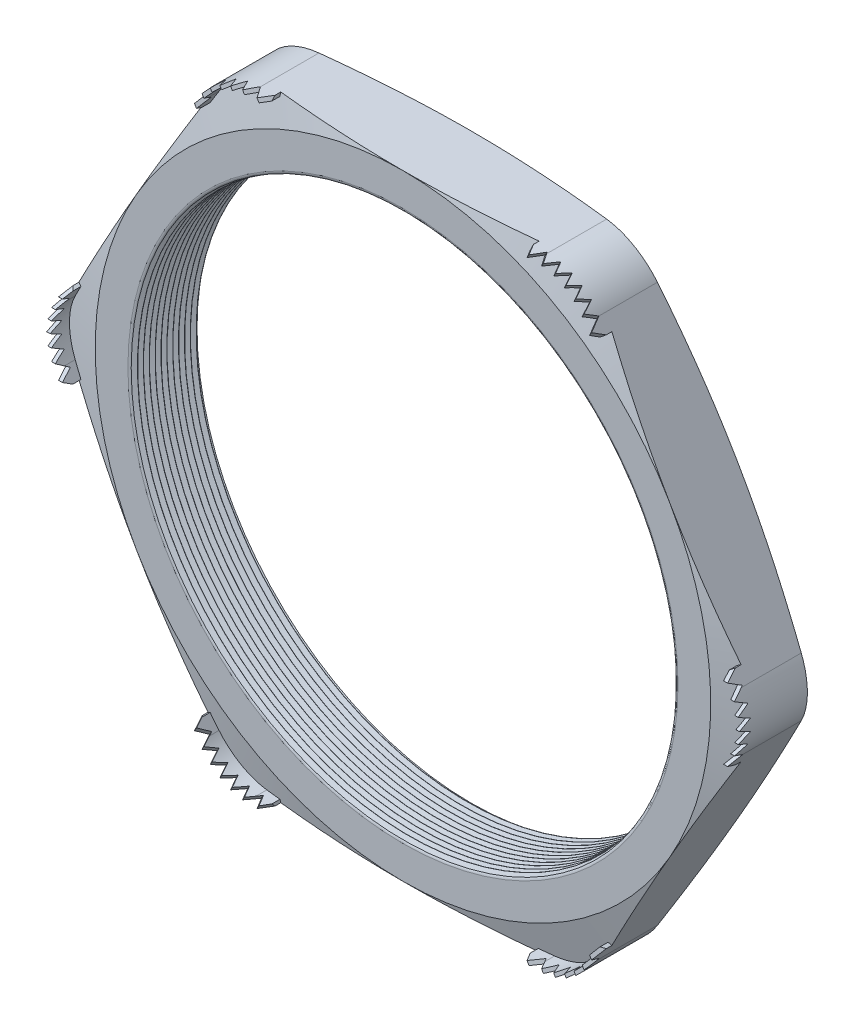
SolidWorks part; units mm, degrees
ref_plane "Front Plane" through (0, 0, 0) normal (0, 0, 1) x (1, 0, 0)
ref_plane "Top Plane" through (0, 0, 0) normal (0, 1, 0) x (1, 0, 0)
ref_plane "Right Plane" through (0, 0, 0) normal (1, 0, 0) x (0, 0, -1)
sketch "Sketch1" plane through (0, 0, 0) normal (0, 0, 1) x (1, 0, 0)
  line L1 (-18.4775, 0) -> (-9.2388, -16.002)
  line L2 (-9.2388, -16.002) -> (9.2388, -16.002)
  line L3 (9.2388, -16.002) -> (18.4775, 0)
  line L4 (18.4775, 0) -> (9.2388, 16.002)
  line L5 (9.2388, 16.002) -> (-9.2388, 16.002)
  line L6 (-9.2388, 16.002) -> (-18.4775, 0)
  circle A0 centre (0, 0) radius 16.002 construction
  circle A1 centre (0, 0) radius 14.097
  dimension "TS" = 28.194
  dimension "H" = 32.004
extrude "Extrude1" add sketch "Sketch1" along normal blind 3.556
fillet "Fillet1" radius 3.048 6 edges at (-9.2388, 16.002, 1.778) (-18.4775, 0, 1.778) (-9.2388, -16.002, 1.778) (9.2388, -16.002, 1.778) (18.4775, 0, 1.778) (9.2388, 16.002, 1.778)
sketch "Sketch2" plane through (0, 0, 3.556) normal (0, 0, 1) x (1, 0, 0)
  line L0 (-7.479, 16.002) -> (-6.717, 16.002)
  line L1 (7.479, 16.002) -> (-7.479, 16.002) construction
  line L2 (-10.1186, 14.478) -> (-10.4996, 13.8181)
  line L3 (-10.1186, 14.478) -> (-17.5976, 1.524) construction
  line L4 (-7.479, 15.8242) -> (-6.717, 15.8242)
  line L5 (-9.9647, 14.3891) -> (-10.3457, 13.7292)
  line L6 (-10.4996, 13.8181) -> (-10.3457, 13.7292)
  line L7 (-6.717, 16.002) -> (-6.717, 15.8242)
  arc A0 (-7.479, 15.8242) -> (-9.9647, 14.3891) centre (-7.479, 12.954) ccw
  arc A1 (-7.479, 16.002) -> (-10.1186, 14.478) centre (-7.479, 12.954) ccw construction
  arc A4 (-7.479, 16.002) -> (-10.1186, 14.478) centre (-7.479, 12.954) ccw
  dimension "D1" = 0.762
  dimension "D2" = 0.762
  dimension "OFFSET" = 0.1778
fillet "Fillet3" radius 0.2032 2 edges at (14.097, 0, 0) (14.097, 0, 3.556)
sketch "Sketch3" plane through (0, 0, 0) normal (0, 1, 0) x (1, 0, 0)
  line L0 (-14.097, -3.556) -> (-14.097, -3.2627)
  line L2 (-14.097, -3.2627) -> (-14.351, -3.4094)
  line L3 (-14.351, -3.4094) -> (-14.097, -3.556)
  line L4 (-14.097, -0.2032) -> (-14.097, -3.3528) construction
  line L5 (-10.1186, -3.556) -> (-17.5976, -3.556) construction
  dimension "D1" = 60
  dimension "D2" = 60
  dimension "D3" = 0.254
revolve "Cut-Revolve1" cut sketch "Sketch3" angle 360 about axis through (0, 0, 3.556) along (0, 0, -1)
pattern_linear "LPattern1" count 12 spacing 0.3048 along (0, 0, -1) of "Cut-Revolve1"
sketch "Sketch4" plane through (0, 0, 0) normal (0, 0, -1) x (-1, 0, 0)
  line L0 (-17.5976, 1.524) -> (-10.1186, 14.478) construction
  circle A0 centre (0, 0) radius 16.002
extrude "Cut-Extrude1" cut sketch "Sketch4" against normal through all draft 75 flip side to cut
sketch "Sketch5" plane through (0, 0, 3.556) normal (0, 0, 1) x (1, 0, 0)
  line L0 (7.479, 16.002) -> (-7.479, 16.002) construction
  circle A0 centre (0, 0) radius 16.002
extrude "Cut-Extrude2" cut sketch "Sketch5" against normal through all draft 75 flip side to cut
extrude "Extrude2" add sketch "Sketch2" along normal blind 1.397 and the other way up to next
ref_plane "Plane1" through (-8.5313, 14.7767, 0) normal (0.5, -0.866, 0) x (0.866, 0.5, 0)
sketch "Sketch7" plane through (-8.5313, 14.7767, 0) normal (0.5, -0.866, 0) x (0.866, 0.5, 0)
  line L0 (-2.1839, 3.4861) -> (-1.8791, 4.0729)
  line L1 (-2.1839, 3.1936) -> (-2.1839, 4.953) construction
  line L2 (0, 1.3136) -> (0, 4.0135) construction
  line L4 (-1.8791, 4.0729) -> (-1.5743, 3.4861)
  line L5 (-0.6096, 4.0729) -> (-0.3048, 3.4861)
  line L6 (-1.2192, 4.0729) -> (-0.9144, 3.4861)
  line L7 (-0.3048, 3.4861) -> (0, 4.0729)
  line L8 (0, 4.0729) -> (0.3048, 3.4861)
  line L10 (0.6096, 4.0729) -> (0.9144, 3.4861)
  line L11 (1.2192, 4.0729) -> (1.524, 3.4861)
  line L12 (-1.5743, 3.4861) -> (-1.2192, 4.0729)
  line L13 (-0.9144, 3.4861) -> (-0.6096, 4.0729)
  line L14 (0.3048, 3.4861) -> (0.6096, 4.0729)
  line L15 (1.8791, 4.0729) -> (2.1839, 3.4861)
  line L16 (2.1839, 3.1936) -> (2.1839, 4.953) construction
  line L17 (-2.1839, 3.4861) -> (-2.1839, 4.953)
  line L19 (-2.1839, 4.953) -> (2.1839, 4.953)
  line L20 (2.1839, 4.953) -> (2.1839, 3.4861)
  line L23 (0.9144, 3.4861) -> (1.2192, 4.0729)
  line L25 (1.524, 3.4861) -> (1.8791, 4.0729)
  dimension "D1" = 1.4668
  dimension "D2" = 0.8801
  dimension "D3" = 0.3048
extrude "Cut-Extrude4" cut sketch "Sketch7" against normal through all
pattern_circular "CirPattern1" count 6 over 360 about axis through (0, 0, 0) along (0, 0, 1) of "Extrude2"
pattern_circular "CirPattern2" count 6 over 360 about axis through (0, 0, 0) along (0, 0, 1) of "Cut-Extrude4"
